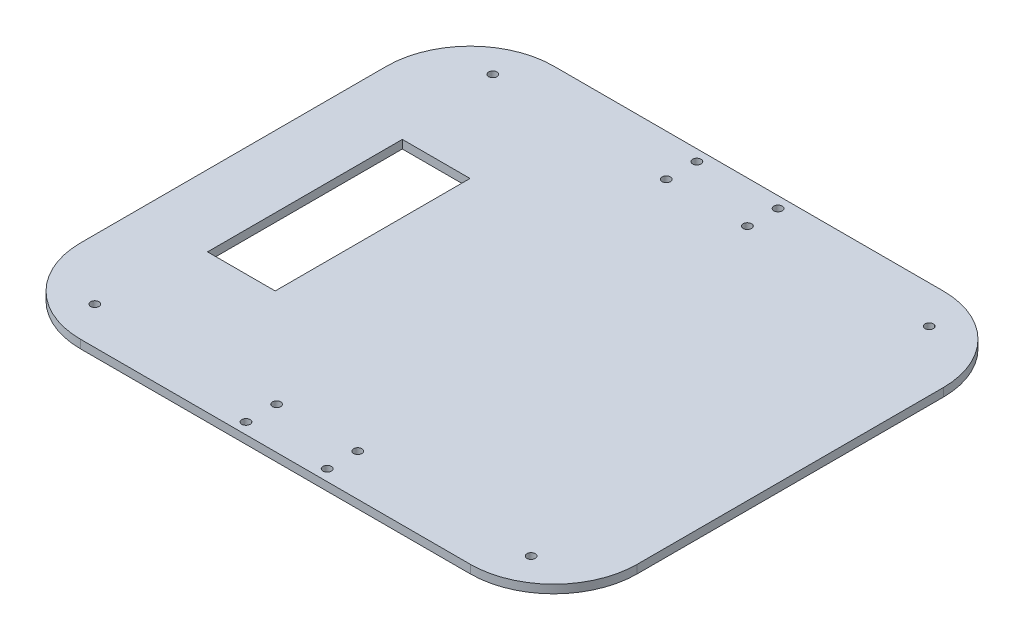
SolidWorks part; units mm, degrees
ref_plane "Front Plane" through (0, 0, 0) normal (0, 0, 1) x (1, 0, 0)
ref_plane "Top Plane" through (0, 0, 0) normal (0, 1, 0) x (1, 0, 0)
ref_plane "Right Plane" through (0, 0, 0) normal (1, 0, 0) x (0, 0, -1)
sketch "Sketch1" plane through (0, 0, 0) normal (0, 1, 0) x (1, 0, 0)
  line L1 (-100, 85) -> (100, 85)
  line L2 (-100, 85) -> (-100, -85)
  line L3 (-100, -85) -> (100, -85)
  line L4 (100, 85) -> (100, -85)
  line L5 (-100, 85) -> (100, -85) construction
  line L6 (-100, -85) -> (100, 85) construction
  point P0 (0, 0)
  dimension "D1" = 200
  dimension "D2" = 170
extrude "Boss-Extrude1" add sketch "Sketch1" along normal blind 3
sketch "Sketch2" plane through (0, 3, 0) normal (0, 1, 0) x (1, 0, 0)
  line L7 (100, 0) -> (-100, 0) construction
  line L8 (100, -85) -> (100, 85) construction
  line L9 (-100, 85) -> (-100, -85) construction
  line L11 (-74.4006, 35) -> (-50.0788, 35)
  line L12 (-74.4006, 35) -> (-74.4006, -35)
  line L13 (-74.4006, -35) -> (-50.0788, -35)
  line L14 (-50.0788, 35) -> (-50.0788, -35)
  line L15 (-74.4006, 35) -> (-50.0788, -35) construction
  line L16 (-74.4006, -35) -> (-50.0788, 35) construction
  point P6 (-62.2397, 0)
  dimension "D1" = 70
extrude "Cut-Extrude1" cut sketch "Sketch2" against normal blind 100
sketch "Sketch3" plane through (0, 3, 0) normal (0, 1, 0) x (1, 0, 0)
  line L0 (-100, -85) -> (100, -85) construction
  line L1 (-100, 85) -> (-100, -85) construction
  line L2 (-100, 0) -> (100, 0) construction
  line L3 (100, -85) -> (100, 85) construction
  line L4 (0, 85) -> (0, -85) construction
  line L5 (100, 85) -> (-100, 85) construction
  circle A0 centre (-78.38, -71.5) radius 1.5
  circle A1 centre (-78.38, 71.5) radius 1.5
  circle A2 centre (78.38, 71.5) radius 1.5
  circle A3 centre (78.38, -71.5) radius 1.5
  dimension "D1" = 13.5
  dimension "D2" = 21.62
extrude "Cut-Extrude2" cut sketch "Sketch3" against normal blind 100
sketch "Sketch4" plane through (0, 3, 0) normal (0, 1, 0) x (1, 0, 0)
  line L0 (-100, 85) -> (-100, -85) construction
  line L1 (-100, -85) -> (100, -85) construction
  line L2 (-100, 0) -> (100, 0) construction
  line L3 (100, -85) -> (100, 85) construction
  line L4 (0, 85) -> (0, -85) construction
  line L5 (100, 85) -> (-100, 85) construction
  line L6 (-100, -75.5) -> (100, -75.5) construction
  circle A0 centre (-14.58, -81) radius 1.5
  circle A1 centre (14.58, -81) radius 1.5
  circle A2 centre (-14.58, -70) radius 1.5
  circle A3 centre (14.58, -70) radius 1.5
  circle A4 centre (-14.58, 81) radius 1.5
  circle A5 centre (-14.58, 70) radius 1.5
  circle A6 centre (14.58, 81) radius 1.5
  circle A7 centre (14.58, 70) radius 1.5
  dimension "D1" = 85.42
  dimension "D2" = 4
  dimension "D3" = 9.5
extrude "Cut-Extrude3" cut sketch "Sketch4" against normal blind 100
fillet "Fillet1" radius 30 4 edges at (-100, 1.5, 85) (-100, 1.5, -85) (100, 1.5, -85) (100, 1.5, 85)
